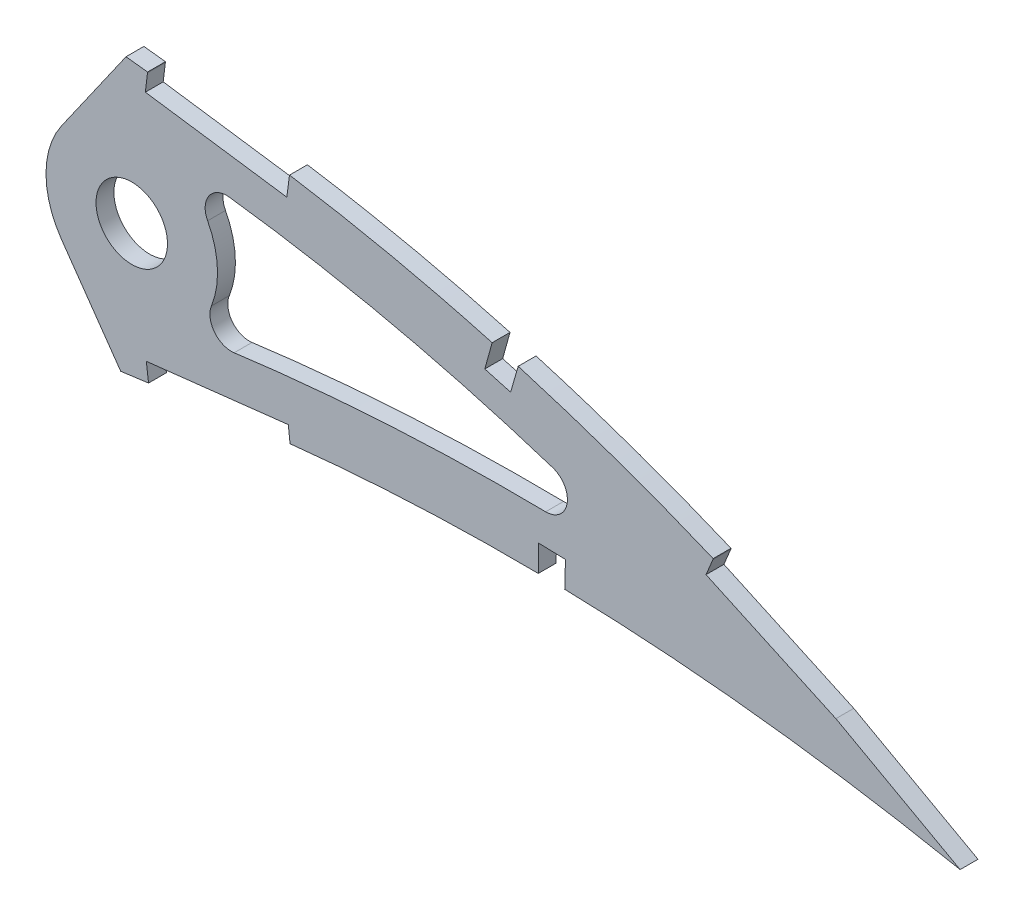
SolidWorks part; units mm, degrees
ref_plane "Front Plane" through (0, 0, 0) normal (0, 0, 1) x (1, 0, 0)
ref_plane "Top Plane" through (0, 0, 0) normal (0, 1, 0) x (1, 0, 0)
ref_plane "Right Plane" through (0, 0, 0) normal (1, 0, 0) x (0, 0, -1)
curve "Curve1"
  spline degree 3 poles (452.1031, 0.7048, 0) (452.0685, 0.7262, 0) (451.9301, 0.8117, 0) (451.6183, 1.003, 0) (451.099, 1.3216, 0) (450.372, 1.7653, 0) (449.438, 2.3329, 0) (448.2963, 3.0204, 0) (446.9478, 3.8257, 0) (445.3928, 4.7448, 0) (443.6314, 5.7736, 0) (441.6643, 6.9077, 0) (439.4916, 8.1409, 0) (437.1143, 9.468, 0) (434.5331, 10.8828, 0) (431.7485, 12.3789, 0) (428.7615, 13.9486, 0) (425.5733, 15.5853, 0) (422.1844, 17.2798, 0) (418.5964, 19.0251, 0) (414.8106, 20.8125, 0) (410.8282, 22.6325, 0) (406.6515, 24.4776, 0) (402.2816, 26.3365, 0) (397.7212, 28.201, 0) (392.972, 30.0605, 0) (388.0369, 31.9065, 0) (382.9178, 33.7272, 0) (377.6186, 35.5144, 0) (372.1418, 37.2567, 0) (366.4913, 38.9446, 0) (360.6704, 40.5671, 0) (354.684, 42.1159, 0) (348.5359, 43.5797, 0) (342.2312, 44.9487, 0) (335.775, 46.2147, 0) (329.1727, 47.3651, 0) (322.4425, 48.3989, 0) (315.6929, 49.2588, 0) (308.9571, 50.1023, 0) (302.2314, 50.8946, 0) (295.4235, 51.6533, 0) (288.5399, 52.3742, 0) (281.5875, 53.055, 0) (274.5733, 53.6928, 0) (267.5046, 54.2857, 0) (260.3883, 54.8303, 0) (253.2318, 55.3259, 0) (246.0422, 55.768, 0) (238.8272, 56.1563, 0) (231.5941, 56.4881, 0) (224.3504, 56.7611, 0) (217.1039, 56.9737, 0) (209.862, 57.1238, 0) (202.6326, 57.2105, 0) (195.4232, 57.2315, 0) (188.2416, 57.1863, 0) (181.0954, 57.0734, 0) (173.9924, 56.8912, 0) (166.9401, 56.6395, 0) (159.9462, 56.3182, 0) (153.0184, 55.9248, 0) (146.164, 55.4618, 0) (139.3909, 54.9271, 0) (132.7063, 54.3206, 0) (126.1174, 53.645, 0) (119.6314, 52.8983, 0) (113.2554, 52.0826, 0) (106.9962, 51.1996, 0) (100.8609, 50.2488, 0) (94.8561, 49.2329, 0) (88.9882, 48.153, 0) (83.2635, 47.0122, 0) (77.6882, 45.8109, 0) (72.2682, 44.5525, 0) (67.0092, 43.2395, 0) (61.9167, 41.874, 0) (56.9959, 40.4594, 0) (52.2519, 38.999, 0) (47.6902, 37.4943, 0) (43.3141, 35.951, 0) (39.1291, 34.3702, 0) (35.1384, 32.7568, 0) (31.3466, 31.113, 0) (27.7567, 29.4439, 0) (24.3726, 27.7512, 0) (21.1967, 26.0397, 0) (18.2324, 24.3122, 0) (15.4823, 22.5717, 0) (12.9477, 20.8227, 0) (10.632, 19.0664, 0) (8.5361, 17.307, 0) (6.6613, 15.5474, 0) (5.0102, 13.7886, 0) (3.5829, 12.0339, 0) (2.3811, 10.2847, 0) (1.4051, 8.5424, 0) (0.6571, 6.8085, 0) (0.1363, 5.084, 0) (-0.1488, 3.3712, 0) (-0.2197, 1.669, 0) (-0.0731, 0.5555, 0) (0, 0, 0) knots 0 0 0 0 0.000254 0.001015 0.002283 0.004057 0.006331 0.009105 0.012374 0.016134 0.02038 0.025106 0.030306 0.035972 0.0421 0.048678 0.055702 0.06316 0.071046 0.07935 0.088063 0.097176 0.106678 0.116562 0.126814 0.137428 0.148394 0.1597 0.171338 0.183298 0.19557 0.208144 0.221012 0.234162 0.247587 0.261277 0.275223 0.289414 0.303771 0.317689 0.331784 0.34604 0.360444 0.374983 0.38964 0.404403 0.419257 0.434187 0.449177 0.464215 0.479284 0.49437 0.509458 0.524532 0.539579 0.554583 0.56953 0.584403 0.599191 0.613877 0.628447 0.642889 0.657186 0.671326 0.685294 0.699078 0.712665 0.726043 0.739198 0.752118 0.764792 0.777208 0.789356 0.801224 0.812804 0.824083 0.835055 0.84571 0.856038 0.866034 0.875689 0.884998 0.893953 0.902553 0.910789 0.918661 0.926166 0.933303 0.940071 0.946475 0.952518 0.958205 0.963547 0.968557 0.97325 0.977651 0.981787 0.985694 0.989415 0.993001 0.996508 1 1 1 1
curve "Curve2"
  spline degree 3 poles (0, 0, 0) (0.1161, -0.5481, 0) (0.3488, -1.6467, 0) (0.9811, -3.2283, 0) (1.8173, -4.7487, 0) (2.8749, -6.2038, 0) (4.147, -7.5932, 0) (5.6306, -8.9184, 0) (7.3243, -10.1787, 0) (9.226, -11.3735, 0) (11.3328, -12.5041, 0) (13.6425, -13.5697, 0) (16.1528, -14.5701, 0) (18.8611, -15.5039, 0) (21.764, -16.3724, 0) (24.8588, -17.1737, 0) (28.1419, -17.9088, 0) (31.6103, -18.5759, 0) (35.26, -19.1755, 0) (39.0874, -19.7075, 0) (43.0885, -20.172, 0) (47.2594, -20.5682, 0) (51.596, -20.8969, 0) (56.0938, -21.1583, 0) (60.7487, -21.3533, 0) (65.556, -21.481, 0) (70.5112, -21.5436, 0) (75.6096, -21.5419, 0) (80.8464, -21.4754, 0) (86.2171, -21.3479, 0) (91.7164, -21.1586, 0) (97.3395, -20.9096, 0) (103.0813, -20.6036, 0) (108.9365, -20.2416, 0) (114.9002, -19.8251, 0) (120.967, -19.3576, 0) (127.1315, -18.8401, 0) (133.3883, -18.2757, 0) (139.7319, -17.6673, 0) (146.1567, -17.0167, 0) (152.6572, -16.327, 0) (159.2275, -15.6004, 0) (165.862, -14.8409, 0) (172.5546, -14.0497, 0) (179.2998, -13.2315, 0) (186.0911, -12.3877, 0) (192.923, -11.5217, 0) (199.7891, -10.6375, 0) (206.6832, -9.7349, 0) (213.5994, -8.8205, 0) (220.5311, -7.8935, 0) (227.4721, -6.9586, 0) (234.4161, -6.0188, 0) (241.3564, -5.0743, 0) (248.2868, -4.1291, 0) (255.2009, -3.1857, 0) (262.0918, -2.2442, 0) (268.9535, -1.3094, 0) (275.779, -0.3811, 0) (282.5619, 0.5389, 0) (289.2958, 1.4477, 0) (295.9744, 2.3443, 0) (302.5907, 3.228, 0) (309.138, 4.0992, 0) (315.5119, 4.9314, 0) (321.6955, 5.769, 0) (327.7099, 6.4556, 0) (333.6493, 7.0417, 0) (339.52, 7.5222, 0) (345.315, 7.9041, 0) (351.0275, 8.19, 0) (356.6509, 8.3839, 0) (362.1779, 8.4917, 0) (367.6017, 8.516, 0) (372.9148, 8.4647, 0) (378.1105, 8.3417, 0) (383.1813, 8.1528, 0) (388.1203, 7.9042, 0) (392.9205, 7.6027, 0) (397.5745, 7.2527, 0) (402.076, 6.8625, 0) (406.4179, 6.4377, 0) (410.5937, 5.9833, 0) (414.5972, 5.5086, 0) (418.4221, 5.0169, 0) (422.0625, 4.5163, 0) (425.5126, 4.0117, 0) (428.7669, 3.5097, 0) (431.8204, 3.015, 0) (434.6681, 2.5342, 0) (437.3055, 2.0718, 0) (439.7281, 1.6323, 0) (441.9324, 1.2212, 0) (443.9143, 0.8406, 0) (445.6709, 0.4968, 0) (447.199, 0.1913, 0) (448.4964, -0.0716, 0) (449.5609, -0.2909, 0) (450.3908, -0.463, 0) (450.9844, -0.5881, 0) (451.3411, -0.6626, 0) (451.4997, -0.6964, 0) (451.5393, -0.7048, 0) knots 0 0 0 0 0.003638 0.007293 0.011028 0.014901 0.018963 0.023258 0.027821 0.032679 0.037853 0.043362 0.049215 0.055422 0.061989 0.068918 0.076211 0.083868 0.091887 0.100266 0.109 0.118085 0.127515 0.137285 0.147388 0.157816 0.168563 0.179619 0.190977 0.202627 0.21456 0.226767 0.239236 0.251959 0.264924 0.27812 0.291536 0.30516 0.318981 0.332985 0.347163 0.361499 0.375981 0.390597 0.405333 0.420175 0.43511 0.450124 0.465203 0.480333 0.495501 0.51069 0.525887 0.541078 0.556247 0.571382 0.586466 0.601485 0.616424 0.631269 0.646007 0.660621 0.675098 0.689423 0.703582 0.716908 0.730009 0.742952 0.755726 0.76832 0.780724 0.792927 0.804916 0.816679 0.828204 0.839475 0.850481 0.861208 0.871639 0.881763 0.891564 0.901027 0.910139 0.918884 0.927249 0.935221 0.942785 0.949928 0.956638 0.962904 0.968712 0.974054 0.978918 0.983297 0.98718 0.990561 0.993433 0.995791 0.99763 0.998946 0.999737 1 1 1 1
sketch "Sketch1" plane through (0, 0, 0) normal (0, 0, 1) x (1, 0, 0)
  line L24 (452.1031, 0.7048) -> (456.094, -1.6764)
  line L25 (451.5393, -0.7048) -> (456.094, -1.6764)
  spline S2 degree 3 poles (-2902.3793, -755.52) (63.6454, 63.6466) (-7.9338, 19.0709) (0.9811, -3.2283) (1.8173, -4.7487) (2.8749, -6.2038) (4.147, -7.5932) (5.6306, -8.9184) (7.3243, -10.1787) (9.226, -11.3735) (11.3328, -12.5041) (13.6425, -13.5697) (16.1528, -14.5701) (18.8611, -15.5039) (21.764, -16.3724) (24.8588, -17.1737) (28.1419, -17.9088) (31.6103, -18.5759) (35.26, -19.1755) (39.0874, -19.7075) (43.0885, -20.172) (47.2594, -20.5682) (51.596, -20.8969) (56.0938, -21.1583) (60.7487, -21.3533) (65.556, -21.481) (70.5112, -21.5436) (75.6096, -21.5419) (80.8464, -21.4754) (86.2171, -21.3479) (91.7164, -21.1586) (97.3395, -20.9096) (103.0813, -20.6036) (108.9365, -20.2416) (114.9002, -19.8251) (120.967, -19.3576) (127.1315, -18.8401) (133.3883, -18.2757) (139.7319, -17.6673) (146.1567, -17.0167) (152.6572, -16.327) (159.2275, -15.6004) (165.862, -14.8409) (172.5546, -14.0497) (179.2998, -13.2315) (186.0911, -12.3877) (192.923, -11.5217) (199.7891, -10.6375) (206.6832, -9.7349) (213.5994, -8.8205) (220.5311, -7.8935) (227.4721, -6.9586) (234.4161, -6.0188) (241.3564, -5.0743) (248.2868, -4.1291) (255.2009, -3.1857) (262.0918, -2.2442) (268.9535, -1.3094) (275.779, -0.3811) (282.5619, 0.5389) (289.2958, 1.4477) (295.9744, 2.3443) (302.5907, 3.228) (309.138, 4.0992) (315.5119, 4.9314) (321.6955, 5.769) (327.7099, 6.4556) (333.6493, 7.0417) (339.52, 7.5222) (345.315, 7.9041) (351.0275, 8.19) (356.6509, 8.3839) (362.1779, 8.4917) (367.6017, 8.516) (372.9148, 8.4647) (378.1105, 8.3417) (383.1813, 8.1528) (388.1203, 7.9042) (392.9205, 7.6027) (397.5745, 7.2527) (402.076, 6.8625) (406.4179, 6.4377) (410.5937, 5.9833) (414.5972, 5.5086) (418.4221, 5.0169) (422.0625, 4.5163) (425.5126, 4.0117) (428.7669, 3.5097) (431.8204, 3.015) (434.6681, 2.5342) (437.3055, 2.0718) (439.7281, 1.6323) (441.9324, 1.2212) (443.9143, 0.8406) (445.6709, 0.4968) (447.199, 0.1913) (448.4964, -0.0716) (449.5609, -0.2909) (450.3908, -0.463) (450.9844, -0.5881) (467.4773, -4.0305) (482.2176, -14.7818) (1120.3699, 2922.8002) knots -0.14446 -0.14446 -0.14446 -0.14446 0.003638 0.007293 0.011028 0.014901 0.018963 0.023258 0.027821 0.032679 0.037853 0.043362 0.049215 0.055422 0.061989 0.068918 0.076211 0.083868 0.091887 0.100266 0.109 0.118085 0.127515 0.137285 0.147388 0.157816 0.168563 0.179619 0.190977 0.202627 0.21456 0.226767 0.239236 0.251959 0.264924 0.27812 0.291536 0.30516 0.318981 0.332985 0.347163 0.361499 0.375981 0.390597 0.405333 0.420175 0.43511 0.450124 0.465203 0.480333 0.495501 0.51069 0.525887 0.541078 0.556247 0.571382 0.586466 0.601485 0.616424 0.631269 0.646007 0.660621 0.675098 0.689423 0.703582 0.716908 0.730009 0.742952 0.755726 0.76832 0.780724 0.792927 0.804916 0.816679 0.828204 0.839475 0.850481 0.861208 0.871639 0.881763 0.891564 0.901027 0.910139 0.918884 0.927249 0.935221 0.942785 0.949928 0.956638 0.962904 0.968712 0.974054 0.978918 0.983297 0.98718 0.990561 0.993433 0.995791 0.99763 0.998946 0.999737 1.107215 1.107215 1.107215 1.107215 only from (0, 0) to (451.5393, -0.7048) construction
  spline S3 degree 3 poles (2072.0463, 2524.7843) (479.969, -24.2918) (467.6474, -8.829) (451.6183, 1.003) (451.099, 1.3216) (450.372, 1.7653) (449.438, 2.3329) (448.2963, 3.0204) (446.9478, 3.8257) (445.3928, 4.7448) (443.6314, 5.7736) (441.6643, 6.9077) (439.4916, 8.1409) (437.1143, 9.468) (434.5331, 10.8828) (431.7485, 12.3789) (428.7615, 13.9486) (425.5733, 15.5853) (422.1844, 17.2798) (418.5964, 19.0251) (414.8106, 20.8125) (410.8282, 22.6325) (406.6515, 24.4776) (402.2816, 26.3365) (397.7212, 28.201) (392.972, 30.0605) (388.0369, 31.9065) (382.9178, 33.7272) (377.6186, 35.5144) (372.1418, 37.2567) (366.4913, 38.9446) (360.6704, 40.5671) (354.684, 42.1159) (348.5359, 43.5797) (342.2312, 44.9487) (335.775, 46.2147) (329.1727, 47.3651) (322.4425, 48.3989) (315.6929, 49.2588) (308.9571, 50.1023) (302.2314, 50.8946) (295.4235, 51.6533) (288.5399, 52.3742) (281.5875, 53.055) (274.5733, 53.6928) (267.5046, 54.2857) (260.3883, 54.8303) (253.2318, 55.3259) (246.0422, 55.768) (238.8272, 56.1563) (231.5941, 56.4881) (224.3504, 56.7611) (217.1039, 56.9737) (209.862, 57.1238) (202.6326, 57.2105) (195.4232, 57.2315) (188.2416, 57.1863) (181.0954, 57.0734) (173.9924, 56.8912) (166.9401, 56.6395) (159.9462, 56.3182) (153.0184, 55.9248) (146.164, 55.4618) (139.3909, 54.9271) (132.7063, 54.3206) (126.1174, 53.645) (119.6314, 52.8983) (113.2554, 52.0826) (106.9962, 51.1996) (100.8609, 50.2488) (94.8561, 49.2329) (88.9882, 48.153) (83.2635, 47.0122) (77.6882, 45.8109) (72.2682, 44.5525) (67.0092, 43.2395) (61.9167, 41.874) (56.9959, 40.4594) (52.2519, 38.999) (47.6902, 37.4943) (43.3141, 35.951) (39.1291, 34.3702) (35.1384, 32.7568) (31.3466, 31.113) (27.7567, 29.4439) (24.3726, 27.7512) (21.1967, 26.0397) (18.2324, 24.3122) (15.4823, 22.5717) (12.9477, 20.8227) (10.632, 19.0664) (8.5361, 17.307) (6.6613, 15.5474) (5.0102, 13.7886) (3.5829, 12.0339) (2.3811, 10.2847) (1.4051, 8.5424) (0.6571, 6.8085) (0.1363, 5.084) (-0.1488, 3.3712) (-1.1473, -20.5831) (81.3582, -38.7525) (-2988.6181, -253.0424) knots -0.115084 -0.115084 -0.115084 -0.115084 0.000254 0.001015 0.002283 0.004057 0.006331 0.009105 0.012374 0.016134 0.02038 0.025106 0.030306 0.035972 0.0421 0.048678 0.055702 0.06316 0.071046 0.07935 0.088063 0.097176 0.106678 0.116562 0.126814 0.137428 0.148394 0.1597 0.171338 0.183298 0.19557 0.208144 0.221012 0.234162 0.247587 0.261277 0.275223 0.289414 0.303771 0.317689 0.331784 0.34604 0.360444 0.374983 0.38964 0.404403 0.419257 0.434187 0.449177 0.464215 0.479284 0.49437 0.509458 0.524532 0.539579 0.554583 0.56953 0.584403 0.599191 0.613877 0.628447 0.642889 0.657186 0.671326 0.685294 0.699078 0.712665 0.726043 0.739198 0.752118 0.764792 0.777208 0.789356 0.801224 0.812804 0.824083 0.835055 0.84571 0.856038 0.866034 0.875689 0.884998 0.893953 0.902553 0.910789 0.918661 0.926166 0.933303 0.940071 0.946475 0.952518 0.958205 0.963547 0.968557 0.97325 0.977651 0.981787 0.985694 0.989415 0.993001 0.996508 1.138367 1.138367 1.138367 1.138367 only from (452.1031, 0.7048) to (0, 0) construction
  spline S4 degree 3 poles (0, 0) (0.1161, -0.5481) (0.3488, -1.6467) (0.9811, -3.2283) (1.8173, -4.7487) (2.8749, -6.2038) (4.147, -7.5932) (5.6306, -8.9184) (7.3243, -10.1787) (9.226, -11.3735) (11.3328, -12.5041) (13.6425, -13.5697) (16.1528, -14.5701) (18.8611, -15.5039) (21.764, -16.3724) (24.8588, -17.1737) (28.1419, -17.9088) (31.6103, -18.5759) (35.26, -19.1755) (39.0874, -19.7075) (43.0885, -20.172) (47.2594, -20.5682) (51.596, -20.8969) (56.0938, -21.1583) (60.7487, -21.3533) (65.556, -21.481) (70.5112, -21.5436) (75.6096, -21.5419) (80.8464, -21.4754) (86.2171, -21.3479) (91.7164, -21.1586) (97.3395, -20.9096) (103.0813, -20.6036) (108.9365, -20.2416) (114.9002, -19.8251) (120.967, -19.3576) (127.1315, -18.8401) (133.3883, -18.2757) (139.7319, -17.6673) (146.1567, -17.0167) (152.6572, -16.327) (159.2275, -15.6004) (165.862, -14.8409) (172.5546, -14.0497) (179.2998, -13.2315) (186.0911, -12.3877) (192.923, -11.5217) (199.7891, -10.6375) (206.6832, -9.7349) (213.5994, -8.8205) (220.5311, -7.8935) (227.4721, -6.9586) (234.4161, -6.0188) (241.3564, -5.0743) (248.2868, -4.1291) (255.2009, -3.1857) (262.0918, -2.2442) (268.9535, -1.3094) (275.779, -0.3811) (282.5619, 0.5389) (289.2958, 1.4477) (295.9744, 2.3443) (302.5907, 3.228) (309.138, 4.0992) (315.5119, 4.9314) (321.6955, 5.769) (327.7099, 6.4556) (333.6493, 7.0417) (339.52, 7.5222) (345.315, 7.9041) (351.0275, 8.19) (356.6509, 8.3839) (362.1779, 8.4917) (367.6017, 8.516) (372.9148, 8.4647) (378.1105, 8.3417) (383.1813, 8.1528) (388.1203, 7.9042) (392.9205, 7.6027) (397.5745, 7.2527) (402.076, 6.8625) (406.4179, 6.4377) (410.5937, 5.9833) (414.5972, 5.5086) (418.4221, 5.0169) (422.0625, 4.5163) (425.5126, 4.0117) (428.7669, 3.5097) (431.8204, 3.015) (434.6681, 2.5342) (437.3055, 2.0718) (439.7281, 1.6323) (441.9324, 1.2212) (443.9143, 0.8406) (445.6709, 0.4968) (447.199, 0.1913) (448.4964, -0.0716) (449.5609, -0.2909) (450.3908, -0.463) (450.9844, -0.5881) (451.3411, -0.6626) (451.4997, -0.6964) (451.5393, -0.7048) knots 0 0 0 0 0.003638 0.007293 0.011028 0.014901 0.018963 0.023258 0.027821 0.032679 0.037853 0.043362 0.049215 0.055422 0.061989 0.068918 0.076211 0.083868 0.091887 0.100266 0.109 0.118085 0.127515 0.137285 0.147388 0.157816 0.168563 0.179619 0.190977 0.202627 0.21456 0.226767 0.239236 0.251959 0.264924 0.27812 0.291536 0.30516 0.318981 0.332985 0.347163 0.361499 0.375981 0.390597 0.405333 0.420175 0.43511 0.450124 0.465203 0.480333 0.495501 0.51069 0.525887 0.541078 0.556247 0.571382 0.586466 0.601485 0.616424 0.631269 0.646007 0.660621 0.675098 0.689423 0.703582 0.716908 0.730009 0.742952 0.755726 0.76832 0.780724 0.792927 0.804916 0.816679 0.828204 0.839475 0.850481 0.861208 0.871639 0.881763 0.891564 0.901027 0.910139 0.918884 0.927249 0.935221 0.942785 0.949928 0.956638 0.962904 0.968712 0.974054 0.978918 0.983297 0.98718 0.990561 0.993433 0.995791 0.99763 0.998946 0.999737 1 1 1 1
  spline S5 degree 3 poles (452.1031, 0.7048) (452.0685, 0.7262) (451.9301, 0.8117) (451.6183, 1.003) (451.099, 1.3216) (450.372, 1.7653) (449.438, 2.3329) (448.2963, 3.0204) (446.9478, 3.8257) (445.3928, 4.7448) (443.6314, 5.7736) (441.6643, 6.9077) (439.4916, 8.1409) (437.1143, 9.468) (434.5331, 10.8828) (431.7485, 12.3789) (428.7615, 13.9486) (425.5733, 15.5853) (422.1844, 17.2798) (418.5964, 19.0251) (414.8106, 20.8125) (410.8282, 22.6325) (406.6515, 24.4776) (402.2816, 26.3365) (397.7212, 28.201) (392.972, 30.0605) (388.0369, 31.9065) (382.9178, 33.7272) (377.6186, 35.5144) (372.1418, 37.2567) (366.4913, 38.9446) (360.6704, 40.5671) (354.684, 42.1159) (348.5359, 43.5797) (342.2312, 44.9487) (335.775, 46.2147) (329.1727, 47.3651) (322.4425, 48.3989) (315.6929, 49.2588) (308.9571, 50.1023) (302.2314, 50.8946) (295.4235, 51.6533) (288.5399, 52.3742) (281.5875, 53.055) (274.5733, 53.6928) (267.5046, 54.2857) (260.3883, 54.8303) (253.2318, 55.3259) (246.0422, 55.768) (238.8272, 56.1563) (231.5941, 56.4881) (224.3504, 56.7611) (217.1039, 56.9737) (209.862, 57.1238) (202.6326, 57.2105) (195.4232, 57.2315) (188.2416, 57.1863) (181.0954, 57.0734) (173.9924, 56.8912) (166.9401, 56.6395) (159.9462, 56.3182) (153.0184, 55.9248) (146.164, 55.4618) (139.3909, 54.9271) (132.7063, 54.3206) (126.1174, 53.645) (119.6314, 52.8983) (113.2554, 52.0826) (106.9962, 51.1996) (100.8609, 50.2488) (94.8561, 49.2329) (88.9882, 48.153) (83.2635, 47.0122) (77.6882, 45.8109) (72.2682, 44.5525) (67.0092, 43.2395) (61.9167, 41.874) (56.9959, 40.4594) (52.2519, 38.999) (47.6902, 37.4943) (43.3141, 35.951) (39.1291, 34.3702) (35.1384, 32.7568) (31.3466, 31.113) (27.7567, 29.4439) (24.3726, 27.7512) (21.1967, 26.0397) (18.2324, 24.3122) (15.4823, 22.5717) (12.9477, 20.8227) (10.632, 19.0664) (8.5361, 17.307) (6.6613, 15.5474) (5.0102, 13.7886) (3.5829, 12.0339) (2.3811, 10.2847) (1.4051, 8.5424) (0.6571, 6.8085) (0.1363, 5.084) (-0.1488, 3.3712) (-0.2197, 1.669) (-0.0731, 0.5555) (0, 0) knots 0 0 0 0 0.000254 0.001015 0.002283 0.004057 0.006331 0.009105 0.012374 0.016134 0.02038 0.025106 0.030306 0.035972 0.0421 0.048678 0.055702 0.06316 0.071046 0.07935 0.088063 0.097176 0.106678 0.116562 0.126814 0.137428 0.148394 0.1597 0.171338 0.183298 0.19557 0.208144 0.221012 0.234162 0.247587 0.261277 0.275223 0.289414 0.303771 0.317689 0.331784 0.34604 0.360444 0.374983 0.38964 0.404403 0.419257 0.434187 0.449177 0.464215 0.479284 0.49437 0.509458 0.524532 0.539579 0.554583 0.56953 0.584403 0.599191 0.613877 0.628447 0.642889 0.657186 0.671326 0.685294 0.699078 0.712665 0.726043 0.739198 0.752118 0.764792 0.777208 0.789356 0.801224 0.812804 0.824083 0.835055 0.84571 0.856038 0.866034 0.875689 0.884998 0.893953 0.902553 0.910789 0.918661 0.926166 0.933303 0.940071 0.946475 0.952518 0.958205 0.963547 0.968557 0.97325 0.977651 0.981787 0.985694 0.989415 0.993001 0.996508 1 1 1 1
extrude "Boss-Extrude1" add sketch "Sketch1" along normal blind 3.175
sketch "Sketch3" plane through (0, 0, 0) normal (0, 0, -1) x (-1, 0, 0)
  circle A1 centre (-299.0384, 26.2554) radius 6.35
extrude "Cut-Extrude2" cut sketch "Sketch3" against normal blind 7.62
sketch "Sketch4" plane through (0, 0, 3.175) normal (0, 0, 1) x (1, 0, 0)
  line L0 (286.5546, 34.9967) -> (298.0139, 51.3624)
  line L1 (286.5546, 17.5141) -> (297.0741, 2.4907)
  line L2 (299.0384, 26.2554) -> (339.6276, 26.2554)
  circle A0 centre (299.0384, 26.2554) radius 6.35 construction
  circle A1 centre (299.0384, 26.2554) radius 6.35
  circle A2 centre (299.0384, 26.2554) radius 15.24
  spline S0 degree 3 poles (-2902.3793, -755.52) (63.6454, 63.6466) (-7.9338, 19.0709) (0.9811, -3.2283) (1.8173, -4.7487) (2.8749, -6.2038) (4.147, -7.5932) (5.6306, -8.9184) (7.3243, -10.1787) (9.226, -11.3735) (11.3328, -12.5041) (13.6425, -13.5697) (16.1528, -14.5701) (18.8611, -15.5039) (21.764, -16.3724) (24.8588, -17.1737) (28.1419, -17.9088) (31.6103, -18.5759) (35.26, -19.1755) (39.0874, -19.7075) (43.0885, -20.172) (47.2594, -20.5682) (51.596, -20.8969) (56.0938, -21.1583) (60.7487, -21.3533) (65.556, -21.481) (70.5112, -21.5436) (75.6096, -21.5419) (80.8464, -21.4754) (86.2171, -21.3479) (91.7164, -21.1586) (97.3395, -20.9096) (103.0813, -20.6036) (108.9365, -20.2416) (114.9002, -19.8251) (120.967, -19.3576) (127.1315, -18.8401) (133.3883, -18.2757) (139.7319, -17.6673) (146.1567, -17.0167) (152.6572, -16.327) (159.2275, -15.6004) (165.862, -14.8409) (172.5546, -14.0497) (179.2998, -13.2315) (186.0911, -12.3877) (192.923, -11.5217) (199.7891, -10.6375) (206.6832, -9.7349) (213.5994, -8.8205) (220.5311, -7.8935) (227.4721, -6.9586) (234.4161, -6.0188) (241.3564, -5.0743) (248.2868, -4.1291) (255.2009, -3.1857) (262.0918, -2.2442) (268.9535, -1.3094) (275.779, -0.3811) (282.5619, 0.5389) (289.2958, 1.4477) (295.9744, 2.3443) (302.5907, 3.228) (309.138, 4.0992) (315.5119, 4.9314) (321.6955, 5.769) (327.7099, 6.4556) (333.6493, 7.0417) (339.52, 7.5222) (345.315, 7.9041) (351.0275, 8.19) (356.6509, 8.3839) (362.1779, 8.4917) (367.6017, 8.516) (372.9148, 8.4647) (378.1105, 8.3417) (383.1813, 8.1528) (388.1203, 7.9042) (392.9205, 7.6027) (397.5745, 7.2527) (402.076, 6.8625) (406.4179, 6.4377) (410.5937, 5.9833) (414.5972, 5.5086) (418.4221, 5.0169) (422.0625, 4.5163) (425.5126, 4.0117) (428.7669, 3.5097) (431.8204, 3.015) (434.6681, 2.5342) (437.3055, 2.0718) (439.7281, 1.6323) (441.9324, 1.2212) (443.9143, 0.8406) (445.6709, 0.4968) (447.199, 0.1913) (448.4964, -0.0716) (449.5609, -0.2909) (450.3908, -0.463) (450.9844, -0.5881) (467.4773, -4.0305) (482.2176, -14.7818) (1120.3699, 2922.8002) knots -0.14446 -0.14446 -0.14446 -0.14446 0.003638 0.007293 0.011028 0.014901 0.018963 0.023258 0.027821 0.032679 0.037853 0.043362 0.049215 0.055422 0.061989 0.068918 0.076211 0.083868 0.091887 0.100266 0.109 0.118085 0.127515 0.137285 0.147388 0.157816 0.168563 0.179619 0.190977 0.202627 0.21456 0.226767 0.239236 0.251959 0.264924 0.27812 0.291536 0.30516 0.318981 0.332985 0.347163 0.361499 0.375981 0.390597 0.405333 0.420175 0.43511 0.450124 0.465203 0.480333 0.495501 0.51069 0.525887 0.541078 0.556247 0.571382 0.586466 0.601485 0.616424 0.631269 0.646007 0.660621 0.675098 0.689423 0.703582 0.716908 0.730009 0.742952 0.755726 0.76832 0.780724 0.792927 0.804916 0.816679 0.828204 0.839475 0.850481 0.861208 0.871639 0.881763 0.891564 0.901027 0.910139 0.918884 0.927249 0.935221 0.942785 0.949928 0.956638 0.962904 0.968712 0.974054 0.978918 0.983297 0.98718 0.990561 0.993433 0.995791 0.99763 0.998946 0.999737 1.107215 1.107215 1.107215 1.107215 only from (0, 0) to (451.5393, -0.7048) construction
  spline S1 degree 3 poles (2072.0463, 2524.7843) (479.969, -24.2918) (467.6474, -8.829) (451.6183, 1.003) (451.099, 1.3216) (450.372, 1.7653) (449.438, 2.3329) (448.2963, 3.0204) (446.9478, 3.8257) (445.3928, 4.7448) (443.6314, 5.7736) (441.6643, 6.9077) (439.4916, 8.1409) (437.1143, 9.468) (434.5331, 10.8828) (431.7485, 12.3789) (428.7615, 13.9486) (425.5733, 15.5853) (422.1844, 17.2798) (418.5964, 19.0251) (414.8106, 20.8125) (410.8282, 22.6325) (406.6515, 24.4776) (402.2816, 26.3365) (397.7212, 28.201) (392.972, 30.0605) (388.0369, 31.9065) (382.9178, 33.7272) (377.6186, 35.5144) (372.1418, 37.2567) (366.4913, 38.9446) (360.6704, 40.5671) (354.684, 42.1159) (348.5359, 43.5797) (342.2312, 44.9487) (335.775, 46.2147) (329.1727, 47.3651) (322.4425, 48.3989) (315.6929, 49.2588) (308.9571, 50.1023) (302.2314, 50.8946) (295.4235, 51.6533) (288.5399, 52.3742) (281.5875, 53.055) (274.5733, 53.6928) (267.5046, 54.2857) (260.3883, 54.8303) (253.2318, 55.3259) (246.0422, 55.768) (238.8272, 56.1563) (231.5941, 56.4881) (224.3504, 56.7611) (217.1039, 56.9737) (209.862, 57.1238) (202.6326, 57.2105) (195.4232, 57.2315) (188.2416, 57.1863) (181.0954, 57.0734) (173.9924, 56.8912) (166.9401, 56.6395) (159.9462, 56.3182) (153.0184, 55.9248) (146.164, 55.4618) (139.3909, 54.9271) (132.7063, 54.3206) (126.1174, 53.645) (119.6314, 52.8983) (113.2554, 52.0826) (106.9962, 51.1996) (100.8609, 50.2488) (94.8561, 49.2329) (88.9882, 48.153) (83.2635, 47.0122) (77.6882, 45.8109) (72.2682, 44.5525) (67.0092, 43.2395) (61.9167, 41.874) (56.9959, 40.4594) (52.2519, 38.999) (47.6902, 37.4943) (43.3141, 35.951) (39.1291, 34.3702) (35.1384, 32.7568) (31.3466, 31.113) (27.7567, 29.4439) (24.3726, 27.7512) (21.1967, 26.0397) (18.2324, 24.3122) (15.4823, 22.5717) (12.9477, 20.8227) (10.632, 19.0664) (8.5361, 17.307) (6.6613, 15.5474) (5.0102, 13.7886) (3.5829, 12.0339) (2.3811, 10.2847) (1.4051, 8.5424) (0.6571, 6.8085) (0.1363, 5.084) (-0.1488, 3.3712) (-1.1473, -20.5831) (81.3582, -38.7525) (-2988.6181, -253.0424) knots -0.115084 -0.115084 -0.115084 -0.115084 0.000254 0.001015 0.002283 0.004057 0.006331 0.009105 0.012374 0.016134 0.02038 0.025106 0.030306 0.035972 0.0421 0.048678 0.055702 0.06316 0.071046 0.07935 0.088063 0.097176 0.106678 0.116562 0.126814 0.137428 0.148394 0.1597 0.171338 0.183298 0.19557 0.208144 0.221012 0.234162 0.247587 0.261277 0.275223 0.289414 0.303771 0.317689 0.331784 0.34604 0.360444 0.374983 0.38964 0.404403 0.419257 0.434187 0.449177 0.464215 0.479284 0.49437 0.509458 0.524532 0.539579 0.554583 0.56953 0.584403 0.599191 0.613877 0.628447 0.642889 0.657186 0.671326 0.685294 0.699078 0.712665 0.726043 0.739198 0.752118 0.764792 0.777208 0.789356 0.801224 0.812804 0.824083 0.835055 0.84571 0.856038 0.866034 0.875689 0.884998 0.893953 0.902553 0.910789 0.918661 0.926166 0.933303 0.940071 0.946475 0.952518 0.958205 0.963547 0.968557 0.97325 0.977651 0.981787 0.985694 0.989415 0.993001 0.996508 1.138367 1.138367 1.138367 1.138367 only from (452.1031, 0.7048) to (0, 0) construction
  spline S2 degree 3 poles (168.2219, -14.5606) (169.6601, -14.3914) (173.3479, -13.9535) (179.2998, -13.2315) (186.0911, -12.3877) (192.923, -11.5217) (199.7891, -10.6375) (206.6832, -9.7349) (213.5994, -8.8205) (220.5311, -7.8935) (227.4721, -6.9586) (234.4161, -6.0188) (241.3564, -5.0743) (248.2868, -4.1291) (255.2009, -3.1857) (262.0918, -2.2442) (268.9535, -1.3094) (275.779, -0.3811) (282.5619, 0.5389) (289.2958, 1.4477) (295.9744, 2.3443) (302.5907, 3.228) (309.138, 4.0992) (315.5119, 4.9314) (321.6955, 5.769) (327.7099, 6.4556) (333.6493, 7.0417) (339.52, 7.5222) (345.315, 7.9041) (351.0275, 8.19) (356.6509, 8.3839) (362.1779, 8.4917) (367.6017, 8.516) (372.9148, 8.4647) (378.1105, 8.3417) (383.1813, 8.1528) (388.1203, 7.9042) (392.9205, 7.6027) (397.5745, 7.2527) (402.076, 6.8625) (406.4179, 6.4377) (410.5937, 5.9833) (414.5972, 5.5086) (418.4221, 5.0169) (422.0625, 4.5163) (425.5126, 4.0117) (428.7669, 3.5097) (431.8204, 3.015) (434.6681, 2.5342) (437.3055, 2.0718) (439.7281, 1.6323) (441.9324, 1.2212) (443.9143, 0.8406) (445.6709, 0.4968) (447.199, 0.1913) (448.4964, -0.0716) (449.5609, -0.2909) (450.3908, -0.463) (450.9844, -0.5881) (451.3411, -0.6626) (451.4997, -0.6964) (451.5393, -0.7048) knots 0.381178 0.381178 0.381178 0.381178 0.390597 0.405333 0.420175 0.43511 0.450124 0.465203 0.480333 0.495501 0.51069 0.525887 0.541078 0.556247 0.571382 0.586466 0.601485 0.616424 0.631269 0.646007 0.660621 0.675098 0.689423 0.703582 0.716908 0.730009 0.742952 0.755726 0.76832 0.780724 0.792927 0.804916 0.816679 0.828204 0.839475 0.850481 0.861208 0.871639 0.881763 0.891564 0.901027 0.910139 0.918884 0.927249 0.935221 0.942785 0.949928 0.956638 0.962904 0.968712 0.974054 0.978918 0.983297 0.98718 0.990561 0.993433 0.995791 0.99763 0.998946 0.999737 1 1 1 1
  spline S3 degree 3 poles (452.1031, 0.7048) (452.0685, 0.7262) (451.9301, 0.8117) (451.6183, 1.003) (451.099, 1.3216) (450.372, 1.7653) (449.438, 2.3329) (448.2963, 3.0204) (446.9478, 3.8257) (445.3928, 4.7448) (443.6314, 5.7736) (441.6643, 6.9077) (439.4916, 8.1409) (437.1143, 9.468) (434.5331, 10.8828) (431.7485, 12.3789) (428.7615, 13.9486) (425.5733, 15.5853) (422.1844, 17.2798) (418.5964, 19.0251) (414.8106, 20.8125) (410.8282, 22.6325) (406.6515, 24.4776) (402.2816, 26.3365) (397.7212, 28.201) (392.972, 30.0605) (388.0369, 31.9065) (382.9178, 33.7272) (377.6186, 35.5144) (372.1418, 37.2567) (366.4913, 38.9446) (360.6704, 40.5671) (354.684, 42.1159) (348.5359, 43.5797) (342.2312, 44.9487) (335.775, 46.2147) (329.1727, 47.3651) (322.4425, 48.3989) (315.6929, 49.2588) (308.9571, 50.1023) (302.2314, 50.8946) (295.4235, 51.6533) (288.5399, 52.3742) (281.5875, 53.055) (274.5733, 53.6928) (267.5046, 54.2857) (260.3883, 54.8303) (253.2318, 55.3259) (246.0422, 55.768) (238.8272, 56.1563) (231.5941, 56.4881) (224.3504, 56.7611) (217.1039, 56.9737) (209.862, 57.1238) (202.6326, 57.2105) (195.4232, 57.2315) (188.2416, 57.1863) (181.0954, 57.0734) (173.9924, 56.8912) (166.9401, 56.6395) (159.9462, 56.3182) (154.9124, 56.0324) (152.2104, 55.8618) (151.8175, 55.8367) knots 0 0 0 0 0.000254 0.001015 0.002283 0.004057 0.006331 0.009105 0.012374 0.016134 0.02038 0.025106 0.030306 0.035972 0.0421 0.048678 0.055702 0.06316 0.071046 0.07935 0.088063 0.097176 0.106678 0.116562 0.126814 0.137428 0.148394 0.1597 0.171338 0.183298 0.19557 0.208144 0.221012 0.234162 0.247587 0.261277 0.275223 0.289414 0.303771 0.317689 0.331784 0.34604 0.360444 0.374983 0.38964 0.404403 0.419257 0.434187 0.449177 0.464215 0.479284 0.49437 0.509458 0.524532 0.539579 0.554583 0.56953 0.584403 0.599191 0.613877 0.628447 0.642889 0.645346 0.645346 0.645346 0.645346
  spline S4 degree 3 poles (151.8175, 55.8367) (149.9244, 55.7154) (145.7716, 55.4308) (139.3909, 54.9271) (132.7063, 54.3206) (126.1174, 53.645) (119.6314, 52.8983) (113.2554, 52.0826) (106.9962, 51.1996) (100.8609, 50.2488) (94.8561, 49.2329) (88.9882, 48.153) (83.2635, 47.0122) (77.6882, 45.8109) (72.2682, 44.5525) (67.0092, 43.2395) (61.9167, 41.874) (56.9959, 40.4594) (52.2519, 38.999) (47.6902, 37.4943) (43.3141, 35.951) (39.1291, 34.3702) (35.1384, 32.7568) (31.3466, 31.113) (27.7567, 29.4439) (24.3726, 27.7512) (21.1967, 26.0397) (18.2324, 24.3122) (15.4823, 22.5717) (12.9477, 20.8227) (10.632, 19.0664) (8.5361, 17.307) (6.6613, 15.5474) (5.0102, 13.7886) (3.5829, 12.0339) (2.3811, 10.2847) (1.4051, 8.5424) (0.6571, 6.8085) (0.1363, 5.084) (-0.1488, 3.3712) (-0.2197, 1.669) (-0.0731, 0.5555) (0, 0) knots 0.645346 0.645346 0.645346 0.645346 0.657186 0.671326 0.685294 0.699078 0.712665 0.726043 0.739198 0.752118 0.764792 0.777208 0.789356 0.801224 0.812804 0.824083 0.835055 0.84571 0.856038 0.866034 0.875689 0.884998 0.893953 0.902553 0.910789 0.918661 0.926166 0.933303 0.940071 0.946475 0.952518 0.958205 0.963547 0.968557 0.97325 0.977651 0.981787 0.985694 0.989415 0.993001 0.996508 1 1 1 1 construction
  spline S5 degree 3 poles (0, 0) (0.1161, -0.5481) (0.3488, -1.6467) (0.9811, -3.2283) (1.8173, -4.7487) (2.8749, -6.2038) (4.147, -7.5932) (5.6306, -8.9184) (7.3243, -10.1787) (9.226, -11.3735) (11.3328, -12.5041) (13.6425, -13.5697) (16.1528, -14.5701) (18.8611, -15.5039) (21.764, -16.3724) (24.8588, -17.1737) (28.1419, -17.9088) (31.6103, -18.5759) (35.26, -19.1755) (39.0874, -19.7075) (43.0885, -20.172) (47.2594, -20.5682) (51.596, -20.8969) (56.0938, -21.1583) (60.7487, -21.3533) (65.556, -21.481) (70.5112, -21.5436) (75.6096, -21.5419) (80.8464, -21.4754) (86.2171, -21.3479) (91.7164, -21.1586) (97.3395, -20.9096) (103.0813, -20.6036) (108.9365, -20.2416) (114.9002, -19.8251) (120.967, -19.3576) (127.1315, -18.8401) (133.3883, -18.2757) (139.7319, -17.6673) (146.1567, -17.0167) (152.6572, -16.327) (159.2275, -15.6004) (164.4232, -15.0056) (167.4283, -14.654) (168.2219, -14.5606) knots 0 0 0 0 0.003638 0.007293 0.011028 0.014901 0.018963 0.023258 0.027821 0.032679 0.037853 0.043362 0.049215 0.055422 0.061989 0.068918 0.076211 0.083868 0.091887 0.100266 0.109 0.118085 0.127515 0.137285 0.147388 0.157816 0.168563 0.179619 0.190977 0.202627 0.21456 0.226767 0.239236 0.251959 0.264924 0.27812 0.291536 0.30516 0.318981 0.332985 0.347163 0.361499 0.375981 0.381178 0.381178 0.381178 0.381178 construction
  spline S7 degree 1 poles (446.7634, -7.9388) (152.467, 45.6974) knots 0 0 1 1 construction
  spline S8 degree 3 poles (446.7634, -7.9388) (446.6007, -7.8383) (446.2797, -7.6414) (445.5971, -7.2229) (444.4249, -6.5084) (442.0753, -5.092) (437.3308, -2.2949) (427.7564, 3.0991) (408.1848, 13.1134) (384.9529, 22.6556) (361.0316, 30.1081) (345.8271, 33.8673) (333.568, 36.3143) (325.8222, 37.6208) (319.6883, 38.5059) (314.9637, 39.1092) (310.1593, 39.7135) (303.8248, 40.4842) (295.8675, 41.3918) (283.1431, 42.7272) (267.2126, 44.1705) (248.0782, 45.5268) (222.5471, 46.8081) (190.6187, 47.3598) (165.1742, 46.5113) (152.467, 45.6974) knots 0 0 0 0 0.00126 0.002521 0.005042 0.010084 0.020167 0.040334 0.080668 0.161336 0.201671 0.242005 0.262172 0.282339 0.292422 0.302506 0.312589 0.322673 0.34284 0.363007 0.403341 0.443675 0.484009 0.564677 0.645346 0.645346 0.645346 0.645346
  spline S9 degree 1 poles (167.0349, -4.4702) (453.6588, 9.2316) knots 0 0 1 1 construction
  spline S10 degree 3 poles (167.0349, -4.4702) (178.802, -3.0861) (202.2904, -0.1126) (231.7242, 3.8627) (255.2844, 7.0807) (272.9652, 9.4926) (287.7144, 11.4893) (299.507, 13.0667) (306.8978, 14.0521) (312.7955, 14.8224) (317.1726, 15.4116) (321.7509, 16.0029) (327.8311, 16.6888) (335.4299, 17.4155) (347.6257, 18.2752) (362.8991, 18.7936) (381.2238, 18.5326) (399.4984, 17.4173) (417.6886, 15.4851) (432.7368, 13.23) (443.2171, 11.3337) (448.433, 10.3099) (451.0341, 9.7796) (452.3447, 9.5083) (452.9929, 9.3717) (453.3455, 9.2981) (453.5574, 9.2532) (453.6588, 9.2316) knots 0.381178 0.381178 0.381178 0.381178 0.458531 0.535883 0.57456 0.613236 0.651913 0.671251 0.690589 0.700258 0.709927 0.719596 0.729265 0.748604 0.767942 0.806618 0.845294 0.883971 0.922647 0.961324 0.980662 0.990331 0.995165 0.997583 0.998791 0.999396 1 1 1 1
  dimension "D2" = 30.48
  dimension "D1" = 10.16
  dimension "D3" = 55
  dimension "D4" = 55
extrude "Cut-Extrude3" cut sketch "Sketch4" against normal through all and the other way through all
sketch "Sketch5" plane through (0, 0, 3.175) normal (0, 0, 1) x (1, 0, 0)
  line L0 (326.9992, 47.185) -> (301.8261, 50.7771)
  line L1 (326.9992, 47.185) -> (301.8261, 50.7771)
  line L2 (301.8261, 50.7771) -> (301.4518, 47.6247)
  line L3 (301.8261, 50.7771) -> (301.4518, 47.6247)
  line L4 (363.0423, 39.775) -> (361.7619, 35.1884)
  line L5 (363.0423, 39.775) -> (361.7619, 35.1884)
  line L6 (367.6609, 38.449) -> (363.0423, 39.775)
  line L7 (367.6609, 38.449) -> (363.0423, 39.775)
  line L8 (326.8461, 9.1691) -> (301.6178, 6.2968)
  line L9 (326.8461, 9.1691) -> (301.6178, 6.2968)
  line L10 (301.6178, 6.2968) -> (302.0231, 3.1479)
  line L11 (301.6178, 6.2968) -> (302.0231, 3.1479)
  line L12 (376.0955, 13.0481) -> (371.3356, 13.1771)
  line L13 (376.0955, 13.0481) -> (371.3356, 13.1771)
  line L14 (371.3356, 13.1771) -> (371.2661, 8.4158)
  line L15 (371.3356, 13.1771) -> (371.2661, 8.4158)
  line L16 (447.9135, 3.0789) -> (425.6786, 15.3563)
  line L17 (447.9135, 3.0789) -> (425.6786, 15.3563)
  line L18 (425.3615, 15.5084) -> (402.2907, 26.1258)
  line L19 (425.3615, 15.5084) -> (402.2907, 26.1258)
  line L20 (402.2907, 26.1258) -> (401.0731, 23.1943)
  line L21 (402.2907, 26.1258) -> (401.0731, 23.1943)
  line L22 (446.3789, 0.2995) -> (447.9135, 3.0789)
  line L23 (446.3789, 0.2995) -> (447.9135, 3.0789)
  line L24 (424.1439, 12.5769) -> (446.3789, 0.2995)
  line L25 (424.1439, 12.5769) -> (446.3789, 0.2995)
  line L26 (401.0731, 23.1943) -> (424.1439, 12.5769)
  line L27 (401.0731, 23.1943) -> (424.1439, 12.5769)
  line L28 (301.4518, 47.6247) -> (326.5816, 44.0377)
  line L29 (301.4518, 47.6247) -> (326.5816, 44.0377)
  line L30 (302.0231, 3.1479) -> (327.2063, 6.0157)
  line L31 (302.0231, 3.1479) -> (327.2063, 6.0157)
  line L32 (326.5816, 44.0377) -> (326.9992, 47.185)
  line L33 (326.5816, 44.0377) -> (326.9992, 47.185)
  line L34 (327.2063, 6.0157) -> (326.8461, 9.1691)
  line L35 (327.2063, 6.0157) -> (326.8461, 9.1691)
  line L36 (366.3485, 33.908) -> (367.6609, 38.449)
  line L37 (366.3485, 33.908) -> (367.6609, 38.449)
  line L38 (361.7619, 35.1884) -> (366.3485, 33.908)
  line L39 (361.7619, 35.1884) -> (366.3485, 33.908)
  line L40 (375.9673, 8.3179) -> (376.0955, 13.0481)
  line L41 (375.9673, 8.3179) -> (376.0955, 13.0481)
  line L42 (371.2661, 8.4158) -> (375.9673, 8.3179)
  line L43 (371.2661, 8.4158) -> (375.9673, 8.3179)
  line L44 (301.8261, 50.7771) -> (302.1055, 52.7356)
  line L45 (326.9992, 47.185) -> (327.3487, 49.6345)
  line L46 (367.6609, 38.449) -> (367.9746, 39.5418)
  line L47 (363.0423, 39.775) -> (363.348, 40.8701)
  line L48 (402.2907, 26.1258) -> (403.1408, 29.1708)
  line L49 (403.1408, 29.1708) -> (476.3451, 29.1708)
  line L50 (476.3451, 29.1708) -> (476.3451, -16.2468)
  line L51 (476.3451, -16.2468) -> (446.3789, 0.2995)
  line L52 (302.0231, 3.1479) -> (302.1091, 2.4793)
extrude "Cut-Extrude4" cut sketch "Sketch5" against normal through all
fillet "Fillet1" radius 3.81 3 edges at (397.0995, 17.4734, 1.5875) (304.8158, 40.3579, 1.5875) (308.4267, 14.2505, 1.5875)
